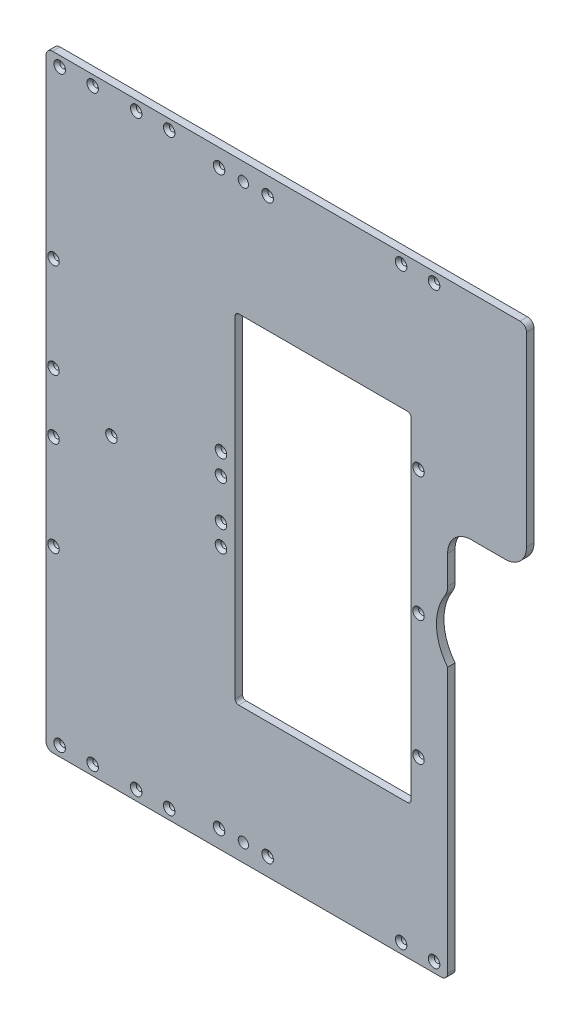
SolidWorks part; units mm, degrees
material "6061-T6 (SS)"
ref_plane "Front Plane" through (0, 0, 0) normal (0, 0, 1) x (1, 0, 0)
ref_plane "Top Plane" through (0, 0, 0) normal (0, 1, 0) x (1, 0, 0)
ref_plane "Right Plane" through (0, 0, 0) normal (1, 0, 0) x (0, 0, -1)
sketch "Sketch1" plane through (0, 0, 0) normal (0, 0, 1) x (1, 0, 0)
  line L0 (32.5, 94.5) -> (32.5, 258)
  line L1 (0, 0) -> (0, 45.5981) construction
  line L2 (0, 0) -> (140.7809, 0) construction
  line L3 (32.5, 258) -> (-375.6002, 258)
  line L4 (-375.6002, 258) -> (-375.6002, -258)
  line L5 (-375.6002, -258) -> (-34.5, -258)
  line L6 (-34.5, -258) -> (-34.5, -27.3084)
  line L7 (14, 85) -> (-13, 85) construction
  line L9 (24, 231.4867) -> (24, 95) construction
  line L10 (-43, 55) -> (-43, 25.7101) construction
  line L11 (14.5, 76.5) -> (-14.5, 76.5)
  line L12 (-34.5, 56.5) -> (-34.5, 32.1053)
  arc A0 (-36.9153, 23.9429) -> (-34.5, -27.3084) centre (0, 0) ccw
  circle A1 centre (0, 0) radius 50.1 construction
  arc A2 (-13, 85) -> (-43, 55) centre (-13, 55) ccw construction
  arc A3 (14, 85) -> (24, 95) centre (14, 95) ccw construction
  arc A4 (-14.5, 76.5) -> (-34.5, 56.5) centre (-14.5, 56.5) ccw
  arc A5 (14.5, 76.5) -> (32.5, 94.5) centre (14.5, 94.5) ccw
  arc A6 (-34.5, 32.1053) -> (-36.9153, 23.9429) centre (-49.5, 32.1053) cw
  point P8 (-375.6002, 0)
  dimension "D1" = 88
  dimension "D6" = 100.2
  dimension "D10" = 30
  dimension "D11" = 10
  dimension "D14" = 20
  dimension "D15" = 18
  dimension "D16" = 15
  dimension "D2" = 32.5
  dimension "D3" = 34.5
  dimension "D4" = 516
  dimension "D5" = 375.6002
  dimension "D7" = 43
  dimension "D8" = 85
  dimension "D9" = 24
  dimension "D12" = 8.5
  dimension "D13" = 8.5
extrude "Boss-Extrude1" add sketch "Sketch1" along normal blind 6.35
sketch "Sketch2" plane through (0, 0, 0) normal (0, 0, -1) x (-1, 0, 0)
  line L0 (0, 0) -> (82.7124, 0) construction
  line L1 (65.6002, 143.8857) -> (214.975, 143.8857)
  line L2 (65.6002, 143.8857) -> (65.6002, -143.8857)
  line L3 (65.6002, -143.8857) -> (214.975, -143.8857)
  line L4 (214.975, 143.8857) -> (214.975, -143.8857)
  line L5 (0, 0) -> (0, 60.4369) construction
  point P7 (65.6002, 0)
  dimension "D1" = 65.6002
  dimension "D2" = 143.8857
  dimension "D3" = 214.975
extrude "Cut-Extrude1" cut sketch "Sketch2" against normal through all
fillet "Fillet1" radius 3 4 edges at (-214.975, -143.8857, 3.175) (-65.6002, -143.8857, 3.175) (-214.975, 143.8857, 3.175) (-65.6002, 143.8857, 3.175)
sketch "top and bottom hole positions" plane through (0, 0, 0) normal (0, 0, -1) x (-1, 0, 0)
  line L0 (350, -249.5) -> (350, -280.2605) construction
  line L1 (271, 249.5) -> (299, 249.5) construction
  line L2 (364, -249.5) -> (336, -249.5) construction
  line L3 (299, -249.5) -> (271, -249.5) construction
  line L4 (0, 0) -> (120.435, 0) construction
  line L5 (0, 0) -> (0, 123.6016) construction
  line L6 (-32.5, 258) -> (375.6002, 258) construction
  line L7 (375.6002, -258) -> (34.5, -258) construction
  line L9 (46, -249.5) -> (74, -249.5) construction
  line L10 (60, -249.5) -> (60, -288.3789) construction
  line L11 (285, -271.2026) -> (285, -328.5325) construction
  point P0 (271, 249.5)
  point P1 (299, 249.5)
  point P3 (299, -249.5)
  point P5 (336, -249.5)
  point P6 (46, -249.5)
  point P7 (364, -249.5)
  point P8 (74, -249.5)
  point P24 (364, 249.5)
  point P25 (336, 249.5)
  point P40 (285, -249.5)
  point P41 (285, 249.5)
  point P42 (74, 249.5)
  point P43 (46, 249.5)
  dimension "D1" = 8.5
  dimension "D2" = 28
  dimension "D3" = 60
  dimension "D4" = 350
  dimension "D5" = 285
  dimension "D6" = 8.5
  dimension "D7" = 8.5
hole_wizard "CSK for #10 Flat Head Machine Screw2" positions "Sketch5" profile "Sketch4" countersink size "#10" standard "ANSI Inch" end condition through all
sketch "Sketch5" plane through (0, 0, 6.35) normal (0, 0, 1) x (1, 0, 0)
  point P0 (-271, 249.5)
  point P3 (-299, 249.5)
  point P6 (-271, -249.5)
  point P9 (-299, -249.5)
  point P12 (-336, -249.5)
  point P15 (-364, -249.5)
  point P18 (-336, 249.5)
  point P20 (-364, 249.5)
  point P28 (-46, -249.5)
  point P30 (-74, -249.5)
  point P35 (-46, 249.5)
  point P37 (-74, 249.5)
sketch "Sketch4" plane through (-271, 249.5, 6.35) normal (1, 0, 0) x (0, -1, 0)
  line L0 (0, 0) -> (0, 6.35)
  line L1 (0, 6.35) -> (2.5527, 6.35)
  line L2 (2.5527, 6.35) -> (2.5527, 2.6882)
  line L3 (2.5527, 2.6882) -> (4.8895, 0)
  line L5 (4.8895, 0) -> (0, 0)
  line L6 (-2.5527, 2.6882) -> (-4.8895, 0) construction
  line L11 (0, -6.35) -> (0, 107.95) construction
  dimension "Thru Hole Dia." = 5.1054
  dimension "Thru Hole Depth" = 6.35
  dimension "Near C'Sink Dia." = 9.779
  dimension "Near C'Sink Angle" = 82
hole_wizard "CSK for #10 Flat Head Machine Screw1" positions "Sketch7" profile "Sketch6" countersink size "#10" standard "ANSI Inch" end condition through all
sketch "Sketch7" plane through (0, 0, 6.35) normal (0, 0, 1) x (1, 0, 0)
  line L0 (-264.275, 143.8857) -> (-411.8881, 143.8857) construction
  line L1 (-211.975, 143.8857) -> (-68.6002, 143.8857) construction
  line L2 (-369.2375, 258) -> (-369.2375, 189.3267) construction
  line L3 (32.5, 258) -> (-375.6002, 258) construction
  line L4 (-375.6002, 258) -> (-375.6002, -258) construction
  line L5 (-214.975, 0) -> (-286.5998, 0) construction
  line L6 (-214.975, -140.8857) -> (-214.975, 140.8857) construction
  line L7 (-114.197, 105.7857) -> (-187.6721, 105.7857) construction
  line L9 (-65.6002, 140.8857) -> (-65.6002, -140.8857) construction
  line L10 (-59.2375, 78.7492) -> (-59.2375, 50.1499) construction
  point P0 (-369.2375, 105.7857)
  point P19 (-369.2375, 25.2785)
  point P23 (-369.2375, -25.2785)
  point P24 (-369.2375, -105.7857)
  point P31 (-59.2375, 105.7857)
  point P35 (-59.2375, 0)
  point P46 (-59.2375, -105.7857)
  dimension "D1" = 6.3627
  dimension "D2" = 38.1
  dimension "D3" = 80.5072
  dimension "D4" = 6.3627
sketch "Sketch6" plane through (-369.2375, 105.7857, 6.35) normal (1, 0, 0) x (0, -1, 0)
  line L0 (0, 0) -> (0, 6.35)
  line L1 (0, 6.35) -> (2.5527, 6.35)
  line L2 (2.5527, 6.35) -> (2.5527, 2.6882)
  line L3 (2.5527, 2.6882) -> (4.8895, 0)
  line L5 (4.8895, 0) -> (0, 0)
  line L6 (-2.5527, 2.6882) -> (-4.8895, 0) construction
  line L11 (0, -6.35) -> (0, 107.95) construction
  dimension "Thru Hole Dia." = 5.1054
  dimension "Thru Hole Depth" = 6.35
  dimension "Near C'Sink Dia." = 9.779
  dimension "Near C'Sink Angle" = 82
sketch "bearing hole positions" plane through (0, 0, 6.35) normal (0, 0, 1) x (1, 0, 0)
  line L0 (0, 0) -> (0, -52.8666) construction
  line L1 (0, 0) -> (43.1334, 0) construction
  line L2 (-227, 17) -> (-227, -35) construction
  line L3 (-227, -9) -> (-189.6307, -9) construction
  point P2 (-227, 17)
  point P5 (-227, -35)
  point P11 (-320, 0)
  point P12 (-227, -17)
  point P13 (-227, 35)
  dimension "D1" = 227
  dimension "D2" = 52
  dimension "D3" = 9
  dimension "D4" = 320
hole_wizard "CSK for #10 Flat Head Machine Screw3" positions "Sketch10" profile "Sketch9" countersink size "#10" standard "ANSI Inch" end condition through all
sketch "Sketch10" plane through (0, 0, 6.35) normal (0, 0, 1) x (1, 0, 0)
  point P4 (-227, 17)
  point P28 (-320, 0)
  point P31 (-227, -35)
  point P35 (-227, -17)
  point P38 (-227, 35)
sketch "Sketch9" plane through (-227, 17, 6.35) normal (1, 0, 0) x (0, -1, 0)
  line L0 (0, 0) -> (0, 6.35)
  line L1 (0, 6.35) -> (2.5527, 6.35)
  line L2 (2.5527, 6.35) -> (2.5527, 2.6882)
  line L3 (2.5527, 2.6882) -> (4.8895, 0)
  line L5 (4.8895, 0) -> (0, 0)
  line L6 (-2.5527, 2.6882) -> (-4.8895, 0) construction
  line L11 (0, -6.35) -> (0, 107.95) construction
  dimension "Thru Hole Dia." = 5.1054
  dimension "Thru Hole Depth" = 6.35
  dimension "Near C'Sink Dia." = 9.779
  dimension "Near C'Sink Angle" = 82
sketch "hole position arm support" plane through (0, 0, 6.35) normal (0, 0, 1) x (1, 0, 0)
  line L0 (0, 0) -> (63.7934, 0) construction
  line L1 (-243.475, -28) -> (-224.475, -28)
  line L2 (-243.475, -28) -> (-243.475, 28)
  line L3 (-243.475, 28) -> (-224.475, 28)
  line L4 (-224.475, -28) -> (-224.475, 28)
  line L5 (-243.475, -28) -> (-224.475, 28) construction
  line L6 (-243.475, 28) -> (-224.475, -28) construction
  line L7 (0, 0) -> (0, 57.1458) construction
  point P0 (-233.975, 0)
  dimension "D1" = 224.475
  dimension "D2" = 19
  dimension "D3" = 56
sketch "hole captured bolt" plane through (0, 0, 6.35) normal (0, 0, 1) x (1, 0, 0)
  line L0 (0, 0) -> (83.2402, 0) construction
  line L1 (0, 0) -> (0, 124.9001) construction
  line L2 (-208, 293.0197) -> (-208, 371.7711) construction
  line L3 (-228.6375, 243) -> (-187.3625, 243) construction
  line L4 (32.5, 258) -> (-375.6002, 258) construction
  line L5 (-228.6375, -243) -> (-187.3625, -243) construction
  point P12 (-208, 243)
  point P13 (-208, -243)
  dimension "D1" = 208
  dimension "D2" = 41.275
  dimension "D3" = 15
hole_wizard "CSK for #10 Flat Head Machine Screw5" positions "Sketch16" profile "Sketch15" countersink size "#10" standard "ANSI Inch" end condition through all
sketch "Sketch16" plane through (0, 0, 6.35) normal (0, 0, 1) x (1, 0, 0)
  point P0 (-228.6375, 243)
  point P1 (-187.3625, 243)
  point P4 (-187.3625, -243)
  point P7 (-228.6375, -243)
sketch "Sketch15" plane through (-228.6375, 243, 6.35) normal (1, 0, 0) x (0, -1, 0)
  line L0 (0, 0) -> (0, 6.35)
  line L1 (0, 6.35) -> (2.4892, 6.35)
  line L2 (2.4892, 6.35) -> (2.4892, 2.7612)
  line L3 (2.4892, 2.7612) -> (4.8895, 0)
  line L5 (4.8895, 0) -> (0, 0)
  line L6 (-2.4892, 2.7612) -> (-4.8895, 0) construction
  line L11 (0, -6.35) -> (0, 107.95) construction
  dimension "Thru Hole Dia." = 4.9784
  dimension "Thru Hole Depth" = 6.35
  dimension "Near C'Sink Dia." = 9.779
  dimension "Near C'Sink Angle" = 82
hole_wizard "5/16 Clearance Hole1" positions "Sketch18" profile "Sketch17" hole size "5/16" standard "ANSI Inch" end condition through all
sketch "Sketch18" plane through (0, 0, 6.35) normal (0, 0, 1) x (1, 0, 0)
  point P0 (-208, 243)
  point P3 (-208, -243)
sketch "Sketch17" plane through (-208, 243, 6.35) normal (1, 0, 0) x (0, -1, 0)
  line L0 (0, 0) -> (0, 6.35)
  line L1 (0, 6.35) -> (4.365, 6.35)
  line L2 (4.365, 6.35) -> (4.365, 0)
  line L5 (4.365, 0) -> (0, 0)
  line L11 (0, -6.35) -> (0, 107.95) construction
  dimension "Thru Hole Dia." = 8.73
  dimension "Thru Hole Depth" = 6.35
fillet "Fillet2" radius 5.5 4 edges at (32.5, 258, 3.175) (-375.6002, 258, 3.175) (-375.6002, -258, 3.175) (-34.5, -258, 3.175)
